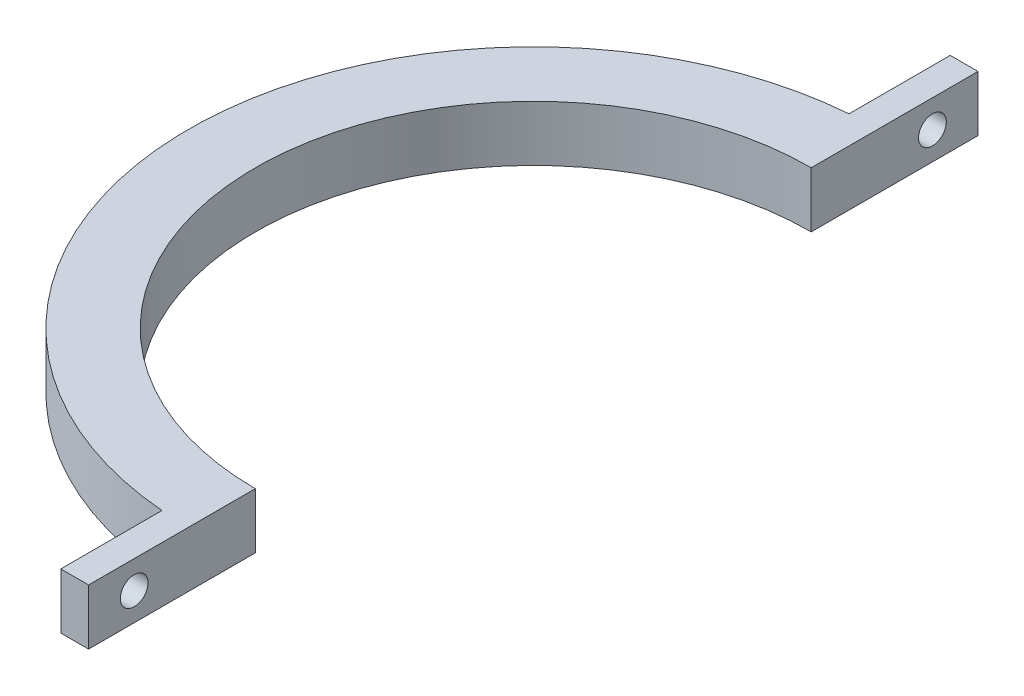
SolidWorks part; units mm, degrees
material "AISI Type 316L stainless steel"
ref_plane "Front Plane" through (0, 0, 0) normal (0, 0, 1) x (1, 0, 0)
ref_plane "Top Plane" through (0, 0, 0) normal (0, 1, 0) x (1, 0, 0)
ref_plane "Right Plane" through (0, 0, 0) normal (1, 0, 0) x (0, 0, -1)
sketch "Sketch1" plane through (0, 0, 0) normal (0, 1, 0) x (1, 0, 0)
  line L0 (0, -25) -> (0, -40)
  line L1 (0, -55) -> (0, 55) construction
  line L2 (0, -40) -> (-2.5, -40)
  line L3 (-2.5, -40) -> (-2.5, -24.8747)
  line L4 (-55, 0) -> (55, 0) construction
  line L5 (0, 40) -> (-2.5, 40)
  line L6 (0, 25) -> (0, 40)
  line L7 (-2.5, 40) -> (-2.5, 24.8747)
  circle A0 centre (0, 0) radius 25
  circle A1 centre (0, 0) radius 31
  dimension "D1" = 50
  dimension "D2" = 6
  dimension "D3" = 15
  dimension "D4" = 2.5
extrude "Boss-Extrude1" add sketch "Sketch1" along normal blind 5 contours L7 A1 L3 A0 | L3 A1 L0 A0 | A1 L3 L2 L0 | L6 A1 L7 A0 | A1 L6 L5 L7
sketch "Sketch5" plane through (-2.5, 0, 0) normal (-1, 0, 0) x (0, 0, 1)
  line L0 (30.899, 5) -> (-30.899, 5) construction
  line L3 (0, -55) -> (0, 55) construction
  line L4 (-30.899, 5) -> (-30.899, 0) construction
  circle A0 centre (-35.899, 2.5) radius 1.25
  circle A1 centre (35.899, 2.5) radius 1.25
  dimension "D1" = 2.5
  dimension "D2" = 2.5
  dimension "D3" = 5
extrude "Cut-Extrude1" cut sketch "Sketch5" against normal through all
